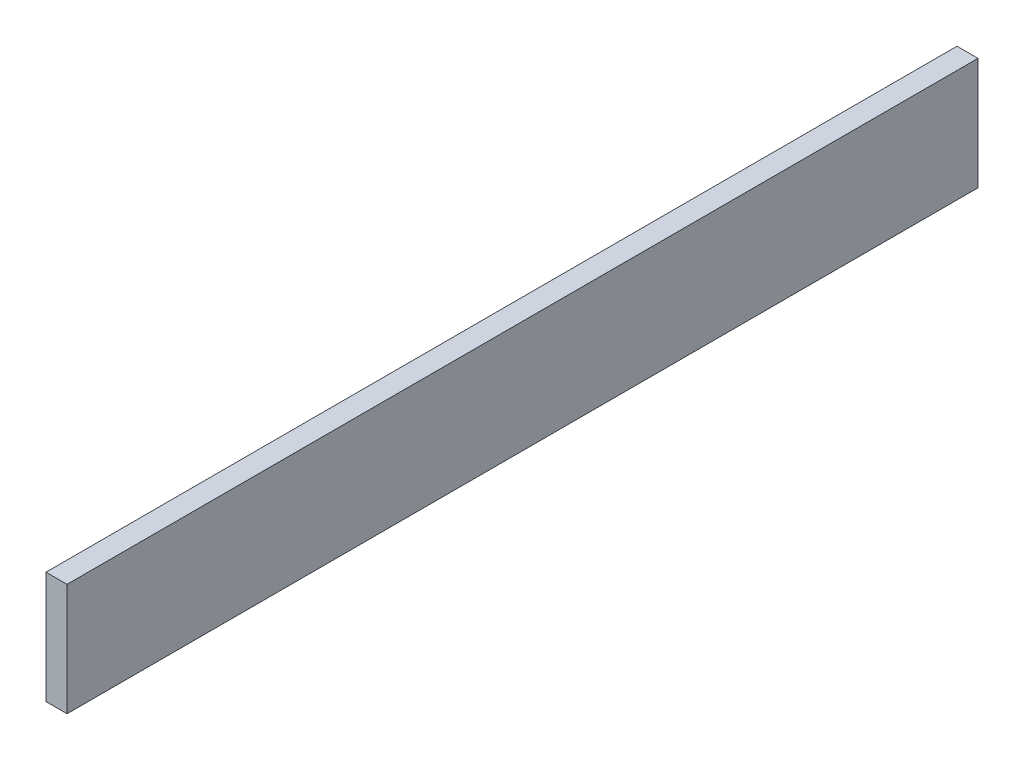
SolidWorks part; units mm, degrees
ref_plane "Front Plane" through (0, 0, 0) normal (0, 0, 1) x (1, 0, 0)
ref_plane "Top Plane" through (0, 0, 0) normal (0, 1, 0) x (1, 0, 0)
ref_plane "Right Plane" through (0, 0, 0) normal (1, 0, 0) x (0, 0, -1)
sketch "Sketch1" plane through (0, 0, 0) normal (1, 0, 0) x (0, 0, -1)
  line L1 (-21.5415, 12.9514) -> (108.4585, 12.9514)
  line L2 (-21.5415, 12.9514) -> (-21.5415, -3.0486)
  line L3 (-21.5415, -3.0486) -> (108.4585, -3.0486)
  line L4 (108.4585, 12.9514) -> (108.4585, -3.0486)
  dimension "D1" = 16
  dimension "D2" = 130
extrude "Boss-Extrude1" add sketch "Sketch1" along normal blind 3
